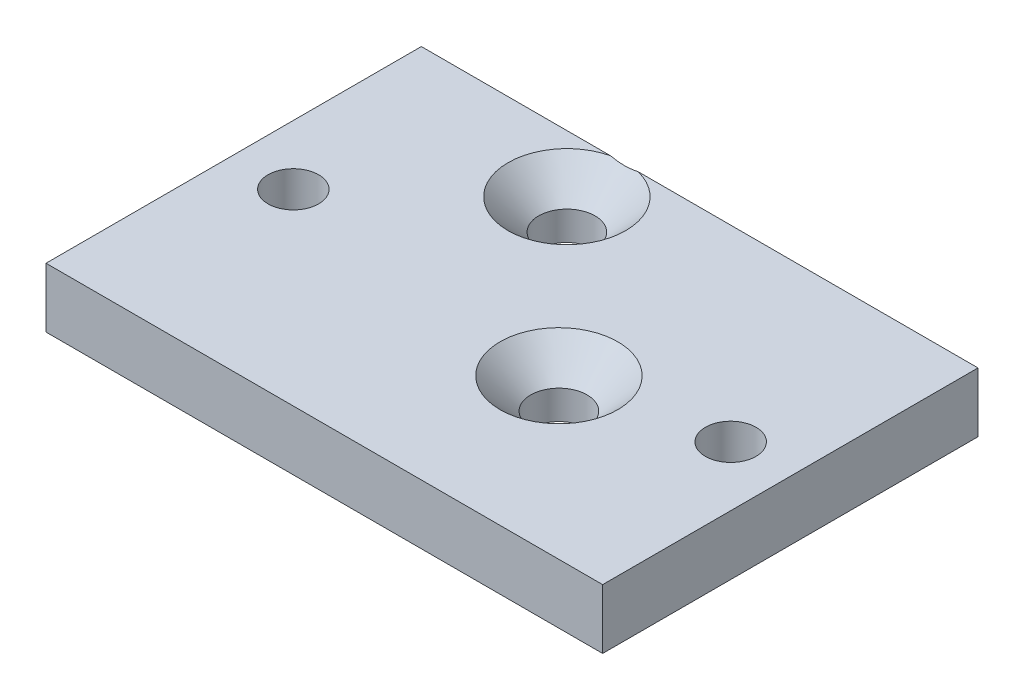
SolidWorks part; units mm, degrees
ref_plane "Front Plane" through (0, 0, 0) normal (0, 0, 1) x (1, 0, 0)
ref_plane "Top Plane" through (0, 0, 0) normal (0, 1, 0) x (1, 0, 0)
ref_plane "Right Plane" through (0, 0, 0) normal (1, 0, 0) x (0, 0, -1)
sketch "Sketch1" plane through (0, 0, 0) normal (0, 1, 0) x (1, 0, 0)
  line L1 (0, 0) -> (44.45, 0)
  line L2 (0, 0) -> (0, 29.972)
  line L3 (0, 29.972) -> (44.45, 29.972)
  line L4 (44.45, 0) -> (44.45, 29.972)
  point P4 (4.7625, 14.986)
  point P5 (39.6875, 14.986)
  point P6 (0, 14.986)
  point P7 (22.225, 0)
  dimension "D1" = 44.45
  dimension "D2" = 29.972
  dimension "D3" = 17.4625
  dimension "D4" = 17.4625
extrude "Extrude1" add sketch "Sketch1" along normal blind 4.7625
hole_wizard "#10-32 Tapped Hole1" positions "Sketch9" profile "Sketch8" tap size "#10-32" standard "Ansi Inch" end condition through all
sketch "Sketch9" plane through (0, 4.7625, 0) normal (0, 1, 0) x (-1, 0, 0)
  line L1 (0, -29.972) -> (0, 0) construction
  line L2 (0, 0) -> (-44.45, 0) construction
  point P0 (-4.7625, -14.986)
  point P1 (0, -14.986)
  point P3 (-39.6875, -14.986)
  dimension "D1" = 4.7625
  dimension "D2" = 14.986
  dimension "D3" = 34.925
sketch "Sketch8" plane through (4.7625, 4.7625, -14.986) normal (1, 0, 0) x (0, 0, 1)
  line L0 (0, 0) -> (0, 4.7625)
  line L1 (0, 4.7625) -> (2.0193, 4.7625)
  line L2 (2.0193, 4.7625) -> (2.0193, 0)
  line L5 (2.0193, 0) -> (0, 0)
  line L11 (0, -6.35) -> (0, 107.95) construction
  dimension "Thru Tap Drill Dia." = 4.0386
  dimension "Thru Tap Drill Depth" = 4.7625
cosmetic thread "Cosmetic Thread3" parameters "D2"=4.826
cosmetic thread "Cosmetic Thread4" parameters "D2"=4.826
hole_wizard "CSK for M4 Flat Head Machine Screw1" positions "Sketch11" profile "Sketch10" countersink size "M4" standard "Ansi Metric" end condition through all
sketch "Sketch11" plane through (0, 4.7625, 0) normal (0, 1, 0) x (-1, 0, 0)
  line L0 (0, 0) -> (-44.45, 0) construction
  line L1 (-44.45, 0) -> (-44.45, -29.972) construction
  line L2 (0, -29.972) -> (0, 0) construction
  point P0 (-28.2575, -12.7)
  point P1 (-16.1925, -25.4)
  dimension "D1" = 25.4
  dimension "D2" = 12.7
  dimension "D3" = 16.1925
  dimension "D4" = 16.1925
  dimension "D5" = 12.065
sketch "Sketch10" plane through (28.2575, 4.7625, -12.7) normal (1, 0, 0) x (0, 0, 1)
  line L0 (0, 0) -> (0, 4.7625)
  line L1 (0, 4.7625) -> (2.25, 4.7625)
  line L2 (2.25, 4.7625) -> (2.25, 2.45)
  line L3 (2.25, 2.45) -> (4.7, 0)
  line L5 (4.7, 0) -> (0, 0)
  line L6 (-2.25, 2.45) -> (-4.7, 0) construction
  line L11 (0, -6.35) -> (0, 107.95) construction
  dimension "Thru Hole Dia." = 4.5
  dimension "Thru Hole Depth" = 4.7625
  dimension "Near C'Sink Dia." = 9.4
  dimension "Near C'Sink Angle" = 90
